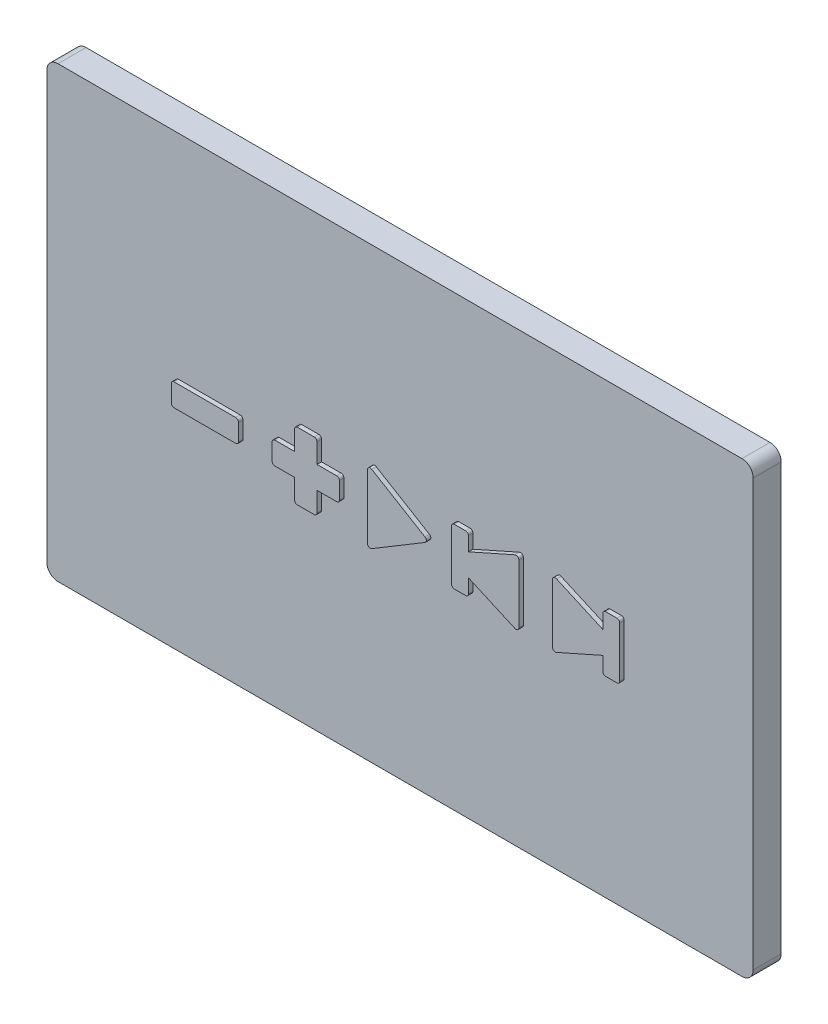
SolidWorks part; units mm, degrees
ref_plane "Front Plane" through (0, 0, 0) normal (0, 0, 1) x (1, 0, 0)
ref_plane "Top Plane" through (0, 0, 0) normal (0, 1, 0) x (1, 0, 0)
ref_plane "Right Plane" through (0, 0, 0) normal (1, 0, 0) x (0, 0, -1)
sketch "Sketch1" plane through (0, 0, 0) normal (0, 0, 1) x (1, 0, 0)
  line L1 (-61, 40) -> (61, 40)
  line L2 (-63, 38) -> (-63, -38)
  line L3 (-61, -40) -> (61, -40)
  line L4 (63, 38) -> (63, -38)
  line L5 (-63, 40) -> (63, -40) construction
  line L6 (-63, -40) -> (63, 40) construction
  arc A0 (61, 40) -> (63, 38) centre (61, 38) cw
  arc A1 (63, -38) -> (61, -40) centre (61, -38) cw
  arc A2 (-61, -40) -> (-63, -38) centre (-61, -38) cw
  arc A3 (-63, 38) -> (-61, 40) centre (-61, 38) cw
  point P0 (0, 0)
  dimension "D1" = 2
sketch "Sketch2" [suppressed] plane through (0, 0, 0) normal (0, 0, 1) x (1, 0, 0)
  line L0 (-5, 5.1169) -> (-5, -5.1169)
  line L1 (-4.2428, -5.5457) -> (4.2854, -0.4287)
  line L2 (4.2854, 0.4287) -> (-4.2428, 5.5457)
  line L3 (-10, -1.5) -> (-10, 1.5)
  line L4 (-10.5, 2) -> (-14, 2)
  line L5 (-14, 2) -> (-14, 5.5)
  line L6 (-14.5, 6) -> (-17.5, 6)
  line L7 (-18, 5.5) -> (-18, 2)
  line L8 (-18, 2) -> (-21.5, 2)
  line L9 (-22, 1.5) -> (-22, -1.5)
  line L10 (-21.5, -2) -> (-18, -2)
  line L11 (-18, -2) -> (-18, -5.5)
  line L12 (-17.5, -6) -> (-14.5, -6)
  line L13 (-14, -5.5) -> (-14, -2)
  line L14 (-14, -2) -> (-10.5, -2)
  line L15 (-28, 1.5) -> (-28, -1.5)
  line L16 (-28.5, -2) -> (-39.5, -2)
  line L17 (-40, -1.5) -> (-40, 1.5)
  line L18 (-39.5, 2) -> (-28.5, 2)
  line L19 (10, 4.5) -> (10, -4.5)
  line L20 (10.5, -5) -> (12.5, -5)
  line L21 (13, -4.5) -> (13, -2)
  line L22 (12.5, 5) -> (10.5, 5)
  line L23 (28, 5.2306) -> (28, -5.2306)
  line L24 (21.2969, 5.6875) -> (13, 2)
  line L25 (13, -2) -> (21.2969, -5.6875)
  line L26 (22, -5.2306) -> (22, 5.2306)
  line L27 (13, 2) -> (13, 4.5)
  line L28 (28.7031, -5.6875) -> (37, -2)
  line L29 (28.7031, 5.6875) -> (37, 2)
  line L30 (37, 2) -> (37, 4.5)
  line L31 (37.5, 5) -> (39.5, 5)
  line L32 (40, 4.5) -> (40, -4.5)
  line L33 (39.5, -5) -> (37.5, -5)
  line L34 (37, -4.5) -> (37, -2)
  arc A0 (-39.5, -2) -> (-40, -1.5) centre (-39.5, -1.5) cw
  arc A1 (-40, 1.5) -> (-39.5, 2) centre (-39.5, 1.5) cw
  arc A2 (-28.5, 2) -> (-28, 1.5) centre (-28.5, 1.5) cw
  arc A3 (-28, -1.5) -> (-28.5, -2) centre (-28.5, -1.5) cw
  arc A4 (-14.5, -6) -> (-14, -5.5) centre (-14.5, -5.5) ccw
  arc A5 (-17.5, -6) -> (-18, -5.5) centre (-17.5, -5.5) cw
  arc A6 (-21.5, -2) -> (-22, -1.5) centre (-21.5, -1.5) cw
  arc A7 (-22, 1.5) -> (-21.5, 2) centre (-21.5, 1.5) cw
  arc A8 (-18, 5.5) -> (-17.5, 6) centre (-17.5, 5.5) cw
  arc A9 (-14.5, 6) -> (-14, 5.5) centre (-14.5, 5.5) cw
  arc A10 (-10.5, 2) -> (-10, 1.5) centre (-10.5, 1.5) cw
  arc A11 (-10.5, -2) -> (-10, -1.5) centre (-10.5, -1.5) ccw
  arc A12 (-4.2428, -5.5457) -> (-5, -5.1169) centre (-4.5, -5.1169) cw
  arc A13 (-5, 5.1169) -> (-4.2428, 5.5457) centre (-4.5, 5.1169) cw
  arc A14 (4.2854, -0.4287) -> (4.2854, 0.4287) centre (4.0282, 0) ccw
  arc A15 (21.2969, 5.6875) -> (22, 5.2306) centre (21.5, 5.2306) cw
  arc A16 (22, -5.2306) -> (21.2969, -5.6875) centre (21.5, -5.2306) cw
  arc A17 (12.5, -5) -> (13, -4.5) centre (12.5, -4.5) ccw
  arc A18 (10.5, -5) -> (10, -4.5) centre (10.5, -4.5) cw
  arc A19 (10, 4.5) -> (10.5, 5) centre (10.5, 4.5) cw
  arc A20 (12.5, 5) -> (13, 4.5) centre (12.5, 4.5) cw
  arc A21 (28.7031, -5.6875) -> (28, -5.2306) centre (28.5, -5.2306) cw
  arc A22 (28, 5.2306) -> (28.7031, 5.6875) centre (28.5, 5.2306) cw
  arc A23 (37.5, -5) -> (37, -4.5) centre (37.5, -4.5) cw
  arc A24 (39.5, -5) -> (40, -4.5) centre (39.5, -4.5) ccw
  arc A25 (37, 4.5) -> (37.5, 5) centre (37.5, 4.5) cw
  arc A26 (40, 4.5) -> (39.5, 5) centre (39.5, 4.5) ccw
  dimension "D1" = 0.5
sketch "Sketch5" [suppressed] plane through (0, 0, 0) normal (0, 0, 1) x (1, 0, 0)
  line L0 (-21, 1) -> (-17, 1)
  line L1 (-39, 1) -> (-29, 1)
  line L2 (-39, 1) -> (-39, -1)
  line L3 (-39, -1) -> (-29, -1)
  line L4 (-29, 1) -> (-29, -1)
  line L5 (-17, 1) -> (-17, 5)
  line L6 (-17, 5) -> (-15, 5)
  line L7 (-15, 5) -> (-15, 1)
  line L8 (-15, 1) -> (-11, 1)
  line L9 (-11, 1) -> (-11, -1)
  line L10 (-11, -1) -> (-15, -1)
  line L11 (-15, -1) -> (-15, -5)
  line L12 (-15, -5) -> (-17, -5)
  line L13 (-17, -5) -> (-17, -1)
  line L14 (-17, -1) -> (-21, -1)
  line L15 (-21, -1) -> (-21, 1)
  line L16 (-4, 4) -> (-4, -4)
  line L17 (-4, -4) -> (3, 0)
  line L18 (3, 0) -> (-4, 4)
  line L19 (29, 4) -> (29, -4)
  line L20 (29, -4) -> (39, 0)
  line L21 (39, 0) -> (29, 4)
  line L22 (11, 0) -> (21, -4)
  line L23 (21, -4) -> (21, 4)
  line L24 (21, 4) -> (11, 0)
sketch "Sketch15" plane through (0, 0, 0) normal (0, 0, 1) x (1, 0, 0)
  circle A0 centre (-52.5, -27.5) radius 1
  circle A1 centre (-52.5, 27.5) radius 1
  circle A2 centre (52.5, -27.5) radius 1
  circle A3 centre (52.5, 27.5) radius 1
  point P0 (0, 0)
sketch "Sketch18" plane through (0, 0, 0) normal (0, 0, 1) x (1, 0, 0)
  circle A0 centre (60, 37) radius 1
  circle A1 centre (60, -37) radius 1
  circle A2 centre (-60, -37) radius 1
  circle A3 centre (-60, 37) radius 1
  circle A4 centre (0, 37) radius 1
  circle A5 centre (0, -37) radius 1
  circle A6 centre (-60, 0) radius 1
  circle A7 centre (60, 0) radius 1
extrude "Boss-Extrude1" add sketch "Sketch1" along normal blind 5
ref_plane "Plane1" through (0, 0, 5) normal (0, 0, 1) x (1, 0, 0)
sketch "Sketch19" plane through (0, 0, 5) normal (0, 0, 1) x (1, 0, 0)
  line L0 (-5, 5.7) -> (-5, -5.7)
  line L1 (-4.2428, -6.1287) -> (5.2572, -0.4287)
  line L2 (5.2572, 0.4287) -> (-4.2428, 6.1287)
  line L3 (-10, -1.5) -> (-10, 1.5)
  line L4 (-10.5, 2) -> (-14, 2)
  line L5 (-14, 2) -> (-14, 5.5)
  line L6 (-14.5, 6) -> (-17.5, 6)
  line L7 (-18, 5.5) -> (-18, 2)
  line L8 (-18, 2) -> (-21.5, 2)
  line L9 (-22, 1.5) -> (-22, -1.5)
  line L10 (-21.5, -2) -> (-18, -2)
  line L11 (-18, -2) -> (-18, -5.5)
  line L12 (-17.5, -6) -> (-14.5, -6)
  line L13 (-14, -5.5) -> (-14, -2)
  line L14 (-14, -2) -> (-10.5, -2)
  line L15 (-28, 1.5) -> (-28, -1.5)
  line L16 (-28.5, -2) -> (-39.5, -2)
  line L17 (-40, -1.5) -> (-40, 1.5)
  line L18 (-39.5, 2) -> (-28.5, 2)
  line L19 (10, 4.5) -> (10, -4.5)
  line L20 (10.5, -5) -> (12.5, -5)
  line L21 (13, -4.5) -> (13, -2)
  line L22 (12.5, 5) -> (10.5, 5)
  line L23 (28, 5.2306) -> (28, -5.2306)
  line L24 (21.2969, 5.6875) -> (13, 2)
  line L25 (13, -2) -> (21.2969, -5.6875)
  line L26 (22, -5.2306) -> (22, 5.2306)
  line L27 (13, 2) -> (13, 4.5)
  line L28 (28.7031, -5.6875) -> (37, -2)
  line L29 (28.7031, 5.6875) -> (37, 2)
  line L30 (37, 2) -> (37, 4.5)
  line L31 (37.5, 5) -> (39.5, 5)
  line L32 (40, 4.5) -> (40, -4.5)
  line L33 (39.5, -5) -> (37.5, -5)
  line L34 (37, -4.5) -> (37, -2)
  arc A0 (-39.5, -2) -> (-40, -1.5) centre (-39.5, -1.5) cw
  arc A1 (-40, 1.5) -> (-39.5, 2) centre (-39.5, 1.5) cw
  arc A2 (-28.5, 2) -> (-28, 1.5) centre (-28.5, 1.5) cw
  arc A3 (-28, -1.5) -> (-28.5, -2) centre (-28.5, -1.5) cw
  arc A4 (-14.5, -6) -> (-14, -5.5) centre (-14.5, -5.5) ccw
  arc A5 (-17.5, -6) -> (-18, -5.5) centre (-17.5, -5.5) cw
  arc A6 (-21.5, -2) -> (-22, -1.5) centre (-21.5, -1.5) cw
  arc A7 (-22, 1.5) -> (-21.5, 2) centre (-21.5, 1.5) cw
  arc A8 (-18, 5.5) -> (-17.5, 6) centre (-17.5, 5.5) cw
  arc A9 (-14.5, 6) -> (-14, 5.5) centre (-14.5, 5.5) cw
  arc A10 (-10.5, 2) -> (-10, 1.5) centre (-10.5, 1.5) cw
  arc A11 (-10.5, -2) -> (-10, -1.5) centre (-10.5, -1.5) ccw
  arc A12 (-4.2428, -6.1287) -> (-5, -5.7) centre (-4.5, -5.7) cw
  arc A13 (-5, 5.7) -> (-4.2428, 6.1287) centre (-4.5, 5.7) cw
  arc A14 (5.2572, -0.4287) -> (5.2572, 0.4287) centre (5, 0) ccw
  arc A15 (21.2969, 5.6875) -> (22, 5.2306) centre (21.5, 5.2306) cw
  arc A16 (22, -5.2306) -> (21.2969, -5.6875) centre (21.5, -5.2306) cw
  arc A17 (12.5, -5) -> (13, -4.5) centre (12.5, -4.5) ccw
  arc A18 (10.5, -5) -> (10, -4.5) centre (10.5, -4.5) cw
  arc A19 (10, 4.5) -> (10.5, 5) centre (10.5, 4.5) cw
  arc A20 (12.5, 5) -> (13, 4.5) centre (12.5, 4.5) cw
  arc A21 (28.7031, -5.6875) -> (28, -5.2306) centre (28.5, -5.2306) cw
  arc A22 (28, 5.2306) -> (28.7031, 5.6875) centre (28.5, 5.2306) cw
  arc A23 (37.5, -5) -> (37, -4.5) centre (37.5, -4.5) cw
  arc A24 (39.5, -5) -> (40, -4.5) centre (39.5, -4.5) ccw
  arc A25 (37, 4.5) -> (37.5, 5) centre (37.5, 4.5) cw
  arc A26 (40, 4.5) -> (39.5, 5) centre (39.5, 4.5) ccw
  dimension "D1" = 0.5
sketch "Sketch20" plane through (0, 0, 5) normal (0, 0, 1) x (1, 0, 0)
  line L35 (-4.1, 4.9935) -> (-4.1, -4.9935)
  line L36 (-4.1, -4.9935) -> (4.2225, 0)
  line L37 (4.2225, 0) -> (-4.1, 4.9935)
  line L38 (-10.9, -1.1) -> (-10.9, 1.1)
  line L39 (-10.9, 1.1) -> (-14.9, 1.1)
  line L40 (-14.9, 1.1) -> (-14.9, 5.1)
  line L41 (-14.9, 5.1) -> (-17.1, 5.1)
  line L42 (-17.1, 5.1) -> (-17.1, 1.1)
  line L43 (-17.1, 1.1) -> (-21.1, 1.1)
  line L44 (-21.1, 1.1) -> (-21.1, -1.1)
  line L45 (-21.1, -1.1) -> (-17.1, -1.1)
  line L46 (-17.1, -1.1) -> (-17.1, -5.1)
  line L47 (-17.1, -5.1) -> (-14.9, -5.1)
  line L48 (-14.9, -5.1) -> (-14.9, -1.1)
  line L49 (-14.9, -1.1) -> (-10.9, -1.1)
  line L50 (-28.9, 1.1) -> (-28.9, -1.1)
  line L51 (-28.9, -1.1) -> (-39.1, -1.1)
  line L52 (-39.1, -1.1) -> (-39.1, 1.1)
  line L53 (-39.1, 1.1) -> (-28.9, 1.1)
  line L54 (10.9, 4.1) -> (10.9, -4.1)
  line L55 (10.9, -4.1) -> (12.1, -4.1)
  line L56 (12.1, -4.1) -> (12.1, -0.6151)
  line L57 (12.1, -0.6151) -> (21.1, -4.6151)
  line L58 (21.1, -4.6151) -> (21.1, 4.6151)
  line L59 (21.1, 4.6151) -> (12.1, 0.6151)
  line L60 (12.1, 0.6151) -> (12.1, 4.1)
  line L61 (12.1, 4.1) -> (10.9, 4.1)
  line L62 (28.9, 4.6151) -> (28.9, -4.6151)
  line L63 (28.9, -4.6151) -> (37.9, -0.6151)
  line L64 (37.9, -4.1) -> (37.9, -0.6151)
  line L65 (39.1, -4.1) -> (37.9, -4.1)
  line L66 (39.1, 4.1) -> (39.1, -4.1)
  line L67 (37.9, 4.1) -> (39.1, 4.1)
  line L68 (37.9, 0.6151) -> (37.9, 4.1)
  line L69 (28.9, 4.6151) -> (37.9, 0.6151)
sketch "Sketch21" plane through (0, 0, 5) normal (0, 0, 1) x (1, 0, 0)
  circle A0 centre (-1, 0) radius 1
  circle A1 centre (-16, 0) radius 1
  circle A2 centre (-34, 0) radius 1
  circle A3 centre (17, 0) radius 1
  circle A4 centre (33, 0) radius 1
sketch "Sketch22" plane through (0, 0, 0) normal (0, 0, 1) x (1, 0, 0)
  circle A0 centre (-34, 0) radius 0.6
  circle A1 centre (-16, 0) radius 0.6
  circle A2 centre (-1, 0) radius 0.6
  circle A3 centre (17, 0) radius 0.6
  circle A4 centre (33, 0) radius 0.6
extrude "Boss-Extrude2" add sketch "Sketch19" along normal blind 0.8
extrude "Cut-Extrude1" cut sketch "Sketch22" along normal blind 2
